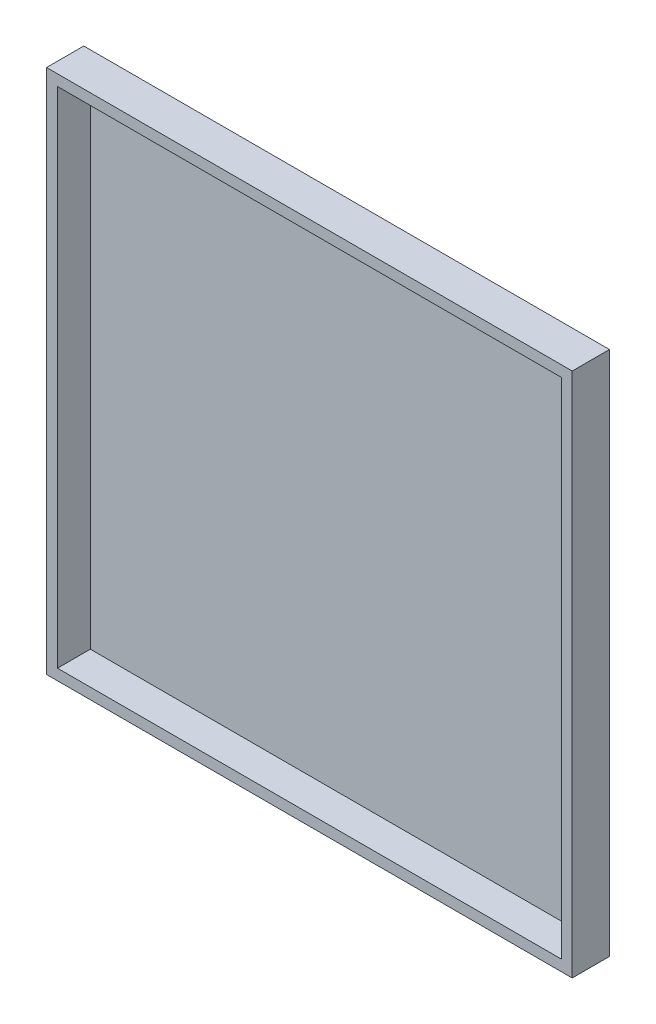
SolidWorks part; units mm, degrees
ref_plane "Front Plane" through (0, 0, 0) normal (0, 0, 1) x (1, 0, 0)
ref_plane "Top Plane" through (0, 0, 0) normal (0, 1, 0) x (1, 0, 0)
ref_plane "Right Plane" through (0, 0, 0) normal (1, 0, 0) x (0, 0, -1)
sketch "Sketch1" plane through (0, 0, 0) normal (0, 0, 1) x (1, 0, 0)
  line L1 (1200, -1200) -> (-1200, -1200)
  line L2 (1200, -1200) -> (1200, 1200)
  line L3 (1200, 1200) -> (-1200, 1200)
  line L4 (-1200, -1200) -> (-1200, 1200)
  line L5 (1200, -1200) -> (-1200, 1200) construction
  line L6 (1200, 1200) -> (-1200, -1200) construction
  point P0 (0, 0)
  dimension "D1" = 2400
  dimension "D2" = 2400
extrude "Boss-Extrude1" add sketch "Sketch1" along normal blind 20
sketch "Sketch2" plane through (0, 0, 20) normal (0, 0, 1) x (1, 0, 0)
  line L11 (1200, -1200) -> (-1200, -1200)
  line L12 (1200, -1200) -> (1200, 1200)
  line L13 (1200, 1200) -> (-1200, 1200)
  line L14 (-1150, -1150) -> (1150, -1150)
  line L15 (1150, -1150) -> (1150, 1150)
  line L16 (1150, 1150) -> (-1150, 1150)
  line L17 (-1150, 1150) -> (-1150, -1150)
  line L18 (-1150, -1150) -> (1150, -1150)
  line L19 (1150, -1150) -> (1150, 1150)
  line L20 (1150, 1150) -> (-1150, 1150)
  line L21 (-1150, 1150) -> (-1150, -1150)
  line L22 (-1200, -1200) -> (-1200, 1200)
  line L23 (1200, -1200) -> (-1200, 1200) construction
  line L24 (1200, 1200) -> (-1200, -1200) construction
  point P0 (0, 0)
  dimension "D1" = 50
extrude "Boss-Extrude2" add sketch "Sketch2" along normal blind 150
